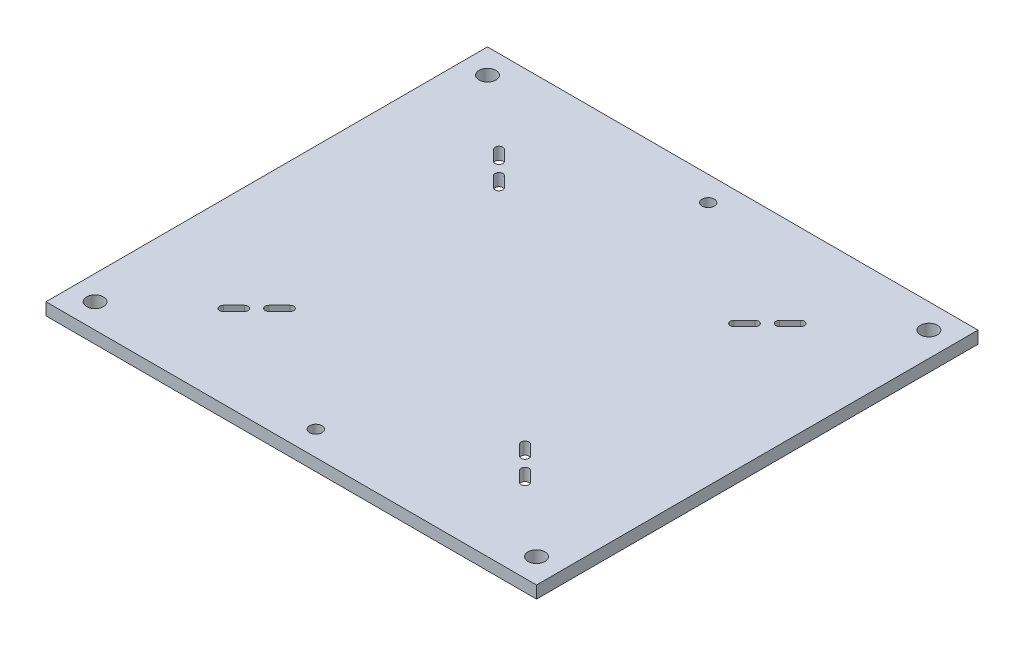
SolidWorks part; units mm, degrees
material "6061-T6 (SS)"
ref_plane "Front Plane" through (0, 0, 0) normal (0, 0, 1) x (1, 0, 0)
ref_plane "Top Plane" through (0, 0, 0) normal (0, 1, 0) x (1, 0, 0)
ref_plane "Right Plane" through (0, 0, 0) normal (1, 0, 0) x (0, 0, -1)
sketch "Sketch1" plane through (0, 0, 0) normal (0, 1, 0) x (1, 0, 0)
  line L1 (0, 0) -> (254, 0)
  line L2 (0, 0) -> (0, -228.6)
  line L3 (0, -228.6) -> (254, -228.6)
  line L4 (254, 0) -> (254, -228.6)
  dimension "D1" = 254
  dimension "D2" = 228.6
extrude "base plate" add sketch "Sketch1" against normal blind 6.35
sketch "center lines" plane through (0, 0, 0) normal (0, 1, 0) x (1, 0, 0)
  line L0 (127, 0) -> (127, -228.6) construction
  line L1 (254, 0) -> (0, 0) construction
  line L2 (0, -228.6) -> (254, -228.6) construction
  line L3 (0, -114.3) -> (254, -114.3) construction
  line L4 (0, 0) -> (0, -228.6) construction
  line L5 (254, -228.6) -> (254, 0) construction
sketch "Sketch3" plane through (0, 0, 0) normal (0, 1, 0) x (1, 0, 0)
  line L0 (36.125, -187.6487) -> (46.9013, -198.425)
  line L1 (46.9013, -198.425) -> (81.0263, -164.3)
  line L2 (81.0263, -164.3) -> (70.25, -153.5237)
  line L3 (70.25, -153.5237) -> (36.125, -187.6487)
  line L4 (48.9222, -185.6278) -> (54.3104, -180.2396) construction
  line L5 (47.508, -184.2135) -> (52.8962, -178.8254)
  line L6 (50.3365, -187.042) -> (55.7246, -181.6538)
  line L7 (0, -228.6) -> (254, -228.6) construction
  line L8 (66.1191, -168.4309) -> (60.7309, -173.8191) construction
  line L9 (67.5333, -169.8451) -> (62.1451, -175.2333)
  line L10 (127, 0) -> (127, -228.6) construction
  line L11 (0, -114.3) -> (254, -114.3) construction
  line L12 (81.0263, -64.3) -> (70.25, -75.0763)
  line L13 (46.9013, -30.175) -> (81.0263, -64.3)
  line L14 (36.125, -40.9513) -> (46.9013, -30.175)
  line L15 (70.25, -75.0763) -> (36.125, -40.9513)
  line L16 (207.0987, -30.175) -> (172.9737, -64.3)
  line L17 (217.875, -40.9513) -> (207.0987, -30.175)
  line L18 (183.75, -75.0763) -> (217.875, -40.9513)
  line L19 (172.9737, -64.3) -> (183.75, -75.0763)
  line L20 (172.9737, -164.3) -> (183.75, -153.5237)
  line L21 (207.0987, -198.425) -> (172.9737, -164.3)
  line L22 (217.875, -187.6487) -> (207.0987, -198.425)
  line L23 (183.75, -153.5237) -> (217.875, -187.6487)
  line L24 (64.7049, -167.0167) -> (59.3167, -172.4049)
  line L25 (48.9222, -42.9722) -> (54.3104, -48.3604) construction
  line L26 (47.508, -44.3865) -> (52.8962, -49.7746)
  line L27 (50.3365, -41.558) -> (55.7246, -46.9462)
  line L28 (66.1191, -60.1691) -> (60.7309, -54.7809) construction
  line L29 (67.5333, -58.7549) -> (62.1451, -53.3667)
  line L30 (64.7049, -61.5833) -> (59.3167, -56.1951)
  line L31 (205.0778, -42.9722) -> (199.6896, -48.3604) construction
  line L32 (206.492, -44.3865) -> (201.1038, -49.7746)
  line L33 (203.6635, -41.558) -> (198.2754, -46.9462)
  line L34 (187.8809, -60.1691) -> (193.2691, -54.7809) construction
  line L35 (186.4667, -58.7549) -> (191.8549, -53.3667)
  line L36 (189.2951, -61.5833) -> (194.6833, -56.1951)
  line L37 (187.8809, -168.4309) -> (193.2691, -173.8191) construction
  line L38 (186.4667, -169.8451) -> (191.8549, -175.2333)
  line L39 (189.2951, -167.0167) -> (194.6833, -172.4049)
  line L40 (205.0778, -185.6278) -> (199.6896, -180.2396) construction
  line L41 (206.492, -184.2135) -> (201.1038, -178.8254)
  line L42 (203.6635, -187.042) -> (198.2754, -181.6538)
  line L43 (70.25, -164.3) -> (70.25, -153.5237)
  line L44 (81.0263, -164.3) -> (70.25, -164.3)
  line L45 (70.25, -64.3) -> (70.25, -75.0763)
  line L46 (81.0263, -64.3) -> (70.25, -64.3)
  line L47 (183.75, -64.3) -> (183.75, -75.0763)
  line L48 (172.9737, -64.3) -> (183.75, -64.3)
  line L49 (183.75, -164.3) -> (183.75, -153.5237)
  line L50 (172.9737, -164.3) -> (183.75, -164.3)
  arc A0 (47.508, -184.2135) -> (50.3365, -187.042) centre (48.9222, -185.6278) ccw
  arc A1 (55.7246, -181.6538) -> (52.8962, -178.8254) centre (54.3104, -180.2396) ccw
  arc A2 (67.5333, -169.8451) -> (64.7049, -167.0167) centre (66.1191, -168.4309) ccw
  arc A3 (59.3167, -172.4049) -> (62.1451, -175.2333) centre (60.7309, -173.8191) ccw
  arc A4 (47.508, -44.3865) -> (50.3365, -41.558) centre (48.9222, -42.9722) cw
  arc A5 (55.7246, -46.9462) -> (52.8962, -49.7746) centre (54.3104, -48.3604) cw
  arc A6 (67.5333, -58.7549) -> (64.7049, -61.5833) centre (66.1191, -60.1691) cw
  arc A7 (59.3167, -56.1951) -> (62.1451, -53.3667) centre (60.7309, -54.7809) cw
  arc A8 (206.492, -44.3865) -> (203.6635, -41.558) centre (205.0778, -42.9722) ccw
  arc A9 (198.2754, -46.9462) -> (201.1038, -49.7746) centre (199.6896, -48.3604) ccw
  arc A10 (186.4667, -58.7549) -> (189.2951, -61.5833) centre (187.8809, -60.1691) ccw
  arc A11 (194.6833, -56.1951) -> (191.8549, -53.3667) centre (193.2691, -54.7809) ccw
  arc A12 (186.4667, -169.8451) -> (189.2951, -167.0167) centre (187.8809, -168.4309) cw
  arc A13 (194.6833, -172.4049) -> (191.8549, -175.2333) centre (193.2691, -173.8191) cw
  arc A14 (206.492, -184.2135) -> (203.6635, -187.042) centre (205.0778, -185.6278) cw
  arc A15 (198.2754, -181.6538) -> (201.1038, -178.8254) centre (199.6896, -180.2396) cw
  point P29 (51.6163, -182.9337)
  point P36 (63.425, -171.125)
  point P44 (51.6163, -45.6663)
  point P51 (63.425, -57.475)
  point P58 (202.3837, -45.6663)
  point P65 (190.575, -57.475)
  point P72 (190.575, -171.125)
  point P79 (202.3837, -182.9337)
  point P84 (55.7246, -178.8254)
  point P85 (59.3167, -175.2333)
  dimension "D6" = 2
  dimension "D10" = 5.08
  dimension "D9" = 5.842
  dimension "D1" = 48.26
  dimension "D2" = 15.24
  dimension "D3" = 45
  dimension "D4" = 100
  dimension "D5" = 113.5
  dimension "D7" = 7.62
  dimension "D8" = 7.62
extrude "slots" cut sketch "Sketch3" against normal through all contours A5 L27 A4 L26 | L33 A9 L32 A8 | L36 A11 L35 A10 | A13 L39 A12 L38 | A15 L42 A14 L41 | L6 A1 L5 A0 | L24 A3 L9 A2 | L30 A7 L29 A6
hole_wizard "Feet connection hole" positions "Sketch6" profile "Sketch7" hole size "1/4-20" standard "PEM® Inch" end condition through all
sketch "Sketch6" plane through (0, 0, 0) normal (0, 1, 0) x (1, 0, 0)
  line L0 (0, -228.6) -> (254, -228.6) construction
  line L1 (0, 0) -> (0, -228.6) construction
  line L2 (254, -228.6) -> (254, 0) construction
  line L3 (254, 0) -> (0, 0) construction
  point P3 (12.7, -215.9)
  point P19 (241.3, -12.7)
  point P33 (12.7, -12.7)
  point P37 (241.3, -215.9)
  dimension "D1" = 12.7
  dimension "D2" = 12.7
  dimension "D3" = 12.7
  dimension "D4" = 12.7
sketch "Sketch7" plane through (12.7, 0, 215.9) normal (1, 0, 0) x (0, 0, 1)
  line L0 (0, 0) -> (0, 6.35)
  line L1 (0, 6.35) -> (4.3688, 6.35)
  line L2 (4.3688, 6.35) -> (4.3688, 0)
  line L5 (4.3688, 0) -> (0, 0)
  line L11 (0, -6.35) -> (0, 107.95) construction
  dimension "Thru Hole Dia." = 8.7376
  dimension "Thru Hole Depth" = 6.35
hole_wizard "Hole for #10 Blind Fasteners (B,BS)1" positions "Sketch17" profile "Sketch18" hole size "#10-32" standard "PEM® Inch" end condition through all
sketch "Sketch17" plane through (0, 0, 0) normal (0, 1, 0) x (1, 0, 0)
  line L0 (0, -228.6) -> (254, -228.6) construction
  line L1 (254, 0) -> (0, 0) construction
  line L2 (254, -228.6) -> (254, 0) construction
  line L3 (0, 0) -> (0, -228.6) construction
  point P0 (127, -215.9)
  point P2 (127, -12.7)
  dimension "D1" = 12.7
  dimension "D2" = 12.7
  dimension "D3" = 127
  dimension "D4" = 127
sketch "Sketch18" plane through (127, 0, 215.9) normal (1, 0, 0) x (0, 0, 1)
  line L0 (0, 0) -> (0, 6.35)
  line L1 (0, 6.35) -> (3.175, 6.35)
  line L2 (3.175, 6.35) -> (3.175, 0)
  line L5 (3.175, 0) -> (0, 0)
  line L11 (0, -6.35) -> (0, 107.95) construction
  dimension "Thru Hole Dia." = 6.35
  dimension "Thru Hole Depth" = 6.35
